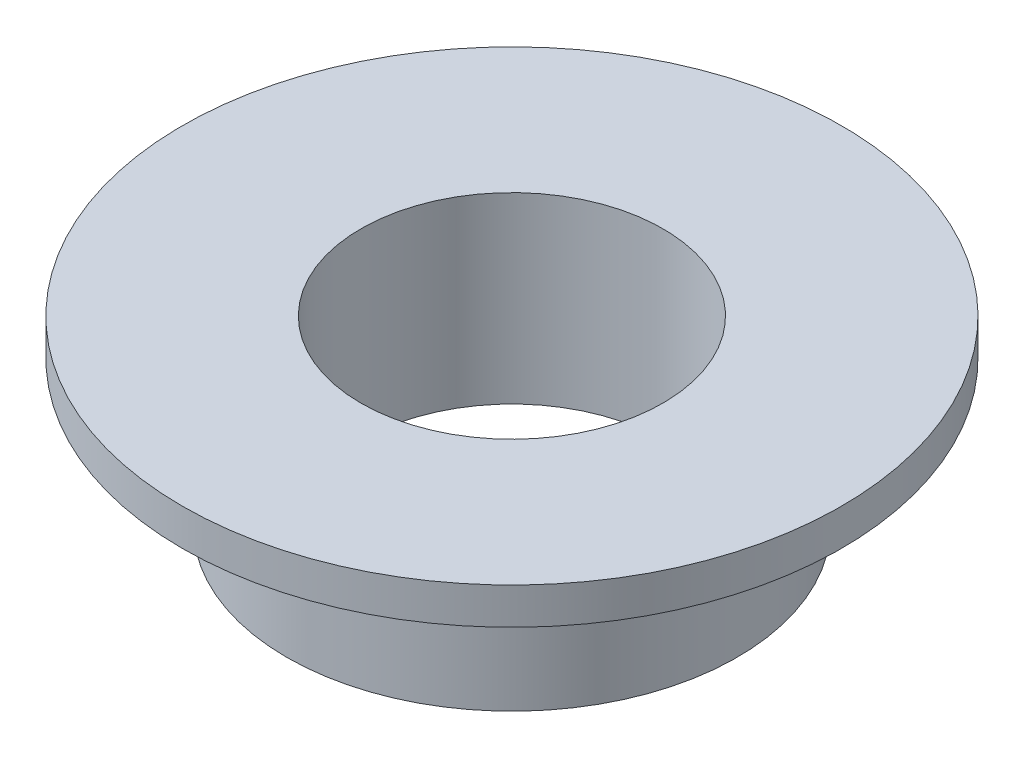
SolidWorks part; units mm, degrees
ref_plane "Front Plane" through (0, 0, 0) normal (0, 0, 1) x (1, 0, 0)
ref_plane "Top Plane" through (0, 0, 0) normal (0, 1, 0) x (1, 0, 0)
ref_plane "Right Plane" through (0, 0, 0) normal (1, 0, 0) x (0, 0, -1)
sketch "Sketch1" plane through (0, 0, 0) normal (0, 1, 0) x (1, 0, 0)
  circle A0 centre (0, 0) radius 6.15
  circle A1 centre (0, 0) radius 4.125
  dimension "D1" = 12.3
  dimension "D2" = 8.25
extrude "Boss-Extrude1" add sketch "Sketch1" along normal blind 4
sketch "Sketch2" plane through (0, 4, 0) normal (0, 1, 0) x (1, 0, 0)
  circle A0 centre (0, 0) radius 4.125 construction
  circle A1 centre (0, 0) radius 4.125
  circle A2 centre (0, 0) radius 9
  dimension "D1" = 18
extrude "Boss-Extrude2" add sketch "Sketch2" along normal blind 1
